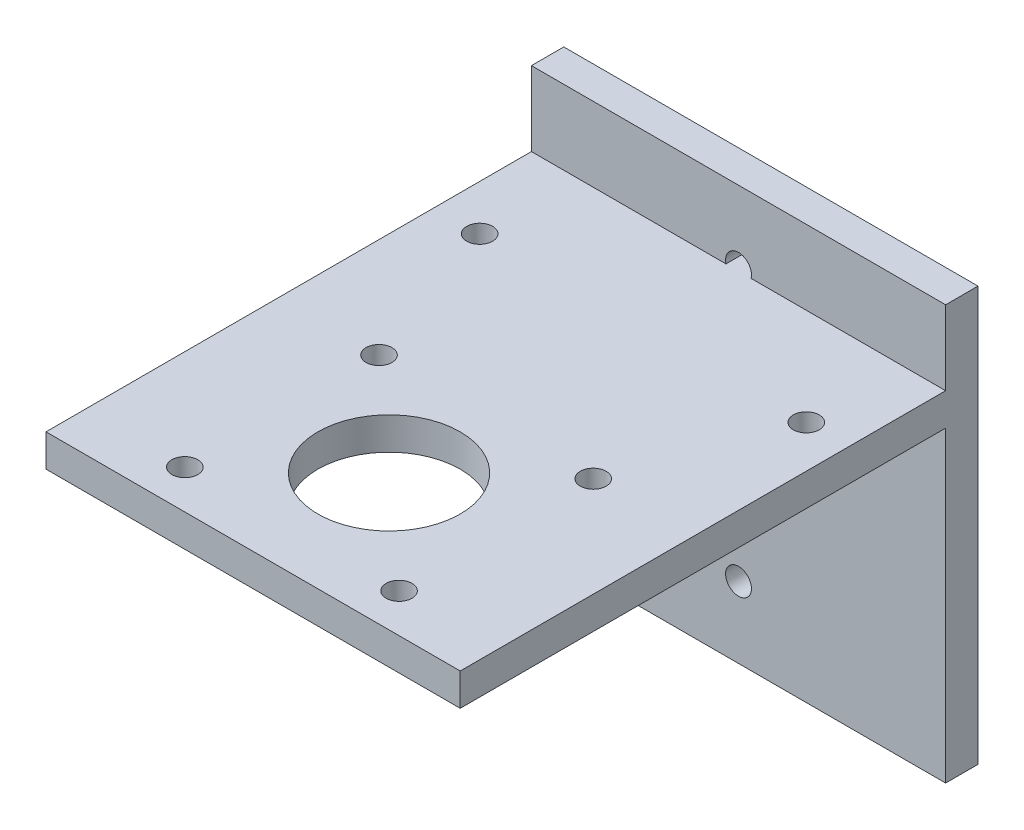
SolidWorks part; units mm, degrees
ref_plane "Plano frontal" through (0, 0, 0) normal (0, 0, 1) x (1, 0, 0)
ref_plane "Plano superior" through (0, 0, 0) normal (0, 1, 0) x (1, 0, 0)
ref_plane "Plano direito" through (0, 0, 0) normal (1, 0, 0) x (0, 0, -1)
sketch "Esboço1" plane through (0, 0, 0) normal (0, 0, 1) x (1, 0, 0)
  line L1 (0, 0) -> (64, 0)
  line L2 (0, 0) -> (0, 64)
  line L3 (0, 64) -> (64, 64)
  line L4 (64, 0) -> (64, 64)
  line L6 (32, 0) -> (32, 64) construction
  line L7 (64, 32) -> (0, 32) construction
  circle A0 centre (32, 42.5) radius 2
  circle A1 centre (32, 32) radius 2
  circle A2 centre (32, 21.5) radius 2
  circle A3 centre (32, 53) radius 2
  circle A4 centre (32, 11) radius 2
  dimension "D4" = 4
  dimension "D5" = 4
  dimension "D6" = 4
  dimension "D10" = 4
  dimension "D11" = 4
  dimension "D1" = 64
  dimension "D2" = 64
  dimension "D3" = 10.5
  dimension "D7" = 10.5
  dimension "D8" = 10.5
  dimension "D9" = 10.5
extrude "Ressalto-extrusão1" add sketch "Esboço1" along normal blind 5
sketch "Esboço2" plane through (0, 0, 0) normal (0, 0, 1) x (1, 0, 0)
  line L0 (0, 32) -> (64, 32) construction
  line L1 (0, 64) -> (0, 0) construction
  line L2 (64, 0) -> (64, 64) construction
  line L4 (0, 52.5) -> (64, 52.5)
  line L5 (0, 52.5) -> (0, 47.5)
  line L6 (0, 47.5) -> (64, 47.5)
  line L7 (64, 52.5) -> (64, 47.5)
  dimension "D1" = 15.5
  dimension "D2" = 5
extrude "Ressalto-extrusão3" add sketch "Esboço2" along normal blind 80
sketch "Esboço3" plane through (0, 0, 0) normal (0, 1, 0) x (1, 0, 0)
  line L0 (32, -80) -> (32, -5) construction
  line L1 (64, -80) -> (0, -80) construction
  line L2 (64, -5) -> (0, -5) construction
  line L3 (0, -74) -> (64, -74) construction
  line L4 (0, -80) -> (0, -5) construction
  line L5 (64, -80) -> (64, -5) construction
  line L6 (0, -44) -> (64, -44) construction
  line L7 (7.0036, -5) -> (7.0036, -80) construction
  line L8 (30.0635, -5) -> (0, -5) construction
  line L9 (57.4658, -5) -> (57.4658, -80) construction
  line L10 (64, -5) -> (33.9365, -5) construction
  circle A0 centre (32, -59) radius 11
  circle A1 centre (15.45, -74) radius 2
  circle A2 centre (48.55, -74) radius 2
  circle A3 centre (15.45, -44) radius 2
  circle A4 centre (48.55, -44) radius 2
  circle A5 centre (7.0036, -20) radius 2
  circle A6 centre (57.4658, -20) radius 2
  dimension "D1" = 22
  dimension "D8" = 4
  dimension "D9" = 4
  dimension "D10" = 4
  dimension "D11" = 4
  dimension "D14" = 4
  dimension "D15" = 4
  dimension "D2" = 21
  dimension "D3" = 16.55
  dimension "D4" = 16.55
  dimension "D5" = 15
  dimension "D6" = 15
  dimension "D7" = 16.55
  dimension "D12" = 15
  dimension "D13" = 15
extrude "Corte-extrusão1" cut sketch "Esboço3" along normal blind 114
